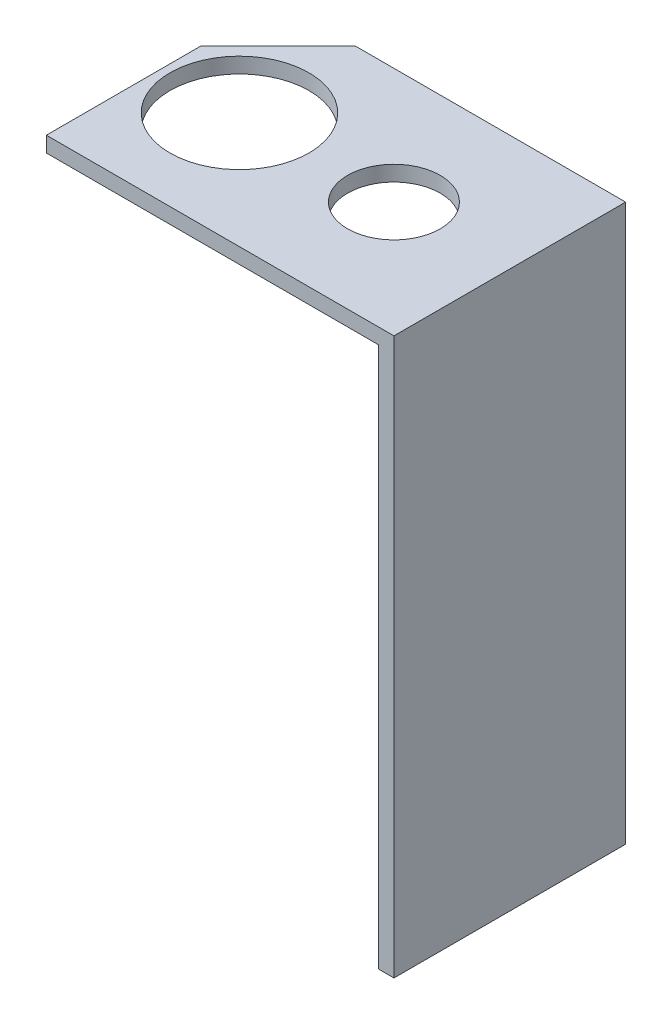
SolidWorks part; units mm, degrees
ref_plane "Front Plane" through (0, 0, 0) normal (0, 0, 1) x (1, 0, 0)
ref_plane "Top Plane" through (0, 0, 0) normal (0, 1, 0) x (1, 0, 0)
ref_plane "Right Plane" through (0, 0, 0) normal (1, 0, 0) x (0, 0, -1)
sketch "Sketch1" plane through (0, 0, 0) normal (0, 1, 0) x (1, 0, 0)
  line L1 (0, 0) -> (45, 0)
  line L2 (0, 0) -> (0, 30)
  line L3 (0, 30) -> (45, 30)
  line L4 (45, 0) -> (45, 30)
  dimension "D1" = 45
  dimension "D2" = 30
extrude "Boss-Extrude1" add sketch "Sketch1" along normal blind 2
sketch "Sketch2" plane through (0, 2, 0) normal (0, 1, 0) x (1, 0, 0)
  line L0 (0, 30) -> (0, 0) construction
  line L1 (0, 0) -> (45, 0) construction
  circle A0 centre (10, 15) radius 9
  circle A1 centre (30, 15) radius 6
  point P4 (0, 0)
  point P7 (0, 0)
  point P9 (8.1825, 27.307)
  dimension "D1" = 12
  dimension "D2" = 18
  dimension "D3" = 20
  dimension "D4" = 10
  dimension "D5" = 15
extrude "Cut-Extrude1" cut sketch "Sketch2" against normal blind 20
sketch "Sketch3" plane through (0, 0, 0) normal (0, -1, 0) x (1, 0, 0)
  line L1 (45, -30) -> (43, -30)
  line L2 (45, -30) -> (45, 0)
  line L3 (45, 0) -> (43, 0)
  line L4 (43, -30) -> (43, 0)
  dimension "D1" = 2
extrude "Boss-Extrude2" add sketch "Sketch3" along normal blind 70
chamfer "Chamfer1" distance 10 angle 45 1 edges at (0, 1, -30)
